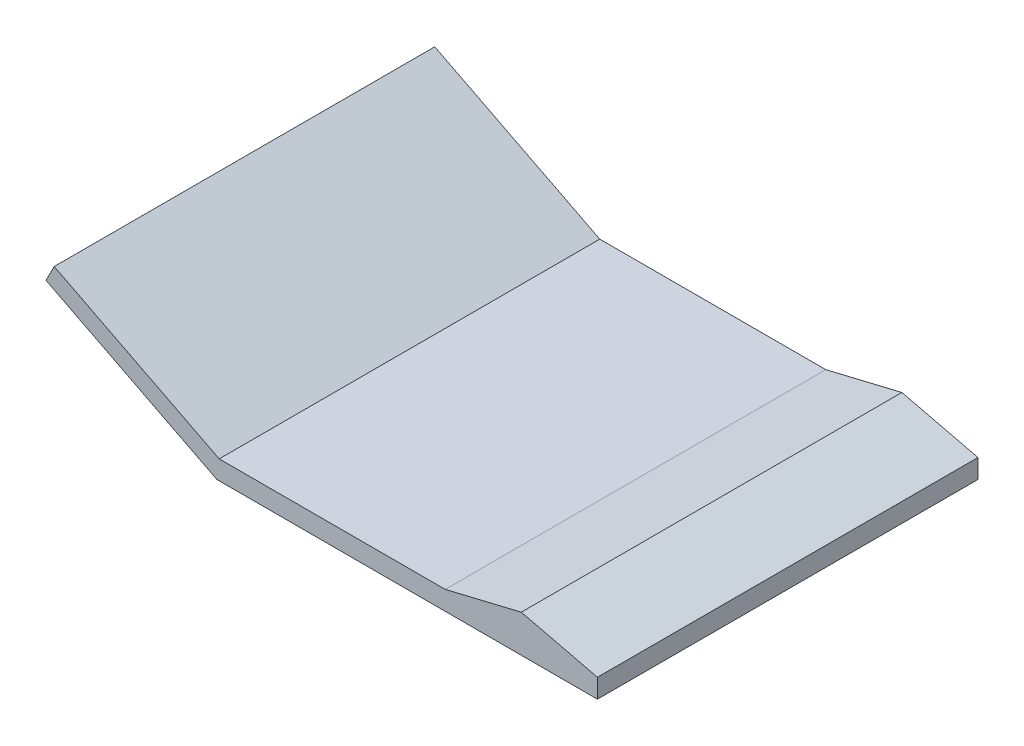
SolidWorks part; units mm, degrees
ref_plane "Plano frontal" through (0, 0, 0) normal (0, 0, 1) x (1, 0, 0)
ref_plane "Plano superior" through (0, 0, 0) normal (0, 1, 0) x (1, 0, 0)
ref_plane "Plano direito" through (0, 0, 0) normal (1, 0, 0) x (0, 0, -1)
sketch "Esboço1" plane through (0, 0, 0) normal (0, 0, 1) x (1, 0, 0)
  line L0 (0, 0) -> (8.6014, 16.8812)
  line L1 (0, 0) -> (400, 0)
  line L2 (0, 0) -> (0, 20)
  line L3 (0, 20) -> (400, 20)
  line L4 (400, 0) -> (400, 20)
  line L5 (0, 0) -> (-179.5586, 91.4897)
  line L6 (8.6014, 16.8812) -> (-170.9572, 108.3709)
  line L7 (-179.5586, 91.4897) -> (-170.9572, 108.3709)
  line L8 (400, 20) -> (320, 39.2063)
  line L9 (320, 39.2063) -> (240, 20)
  dimension "D1" = 400
  dimension "D2" = 20
  dimension "D3" = 63
  dimension "D4" = 80
  dimension "D5" = 80
  dimension "D6" = 153
extrude "Ressalto-extrusão1" add sketch "Esboço1" along normal blind 400 contours L6 L0 L1 L4 L3 | L7 L5 L2 L3 L6 | L0 L6 L3 L2 | L8 L9 L3
